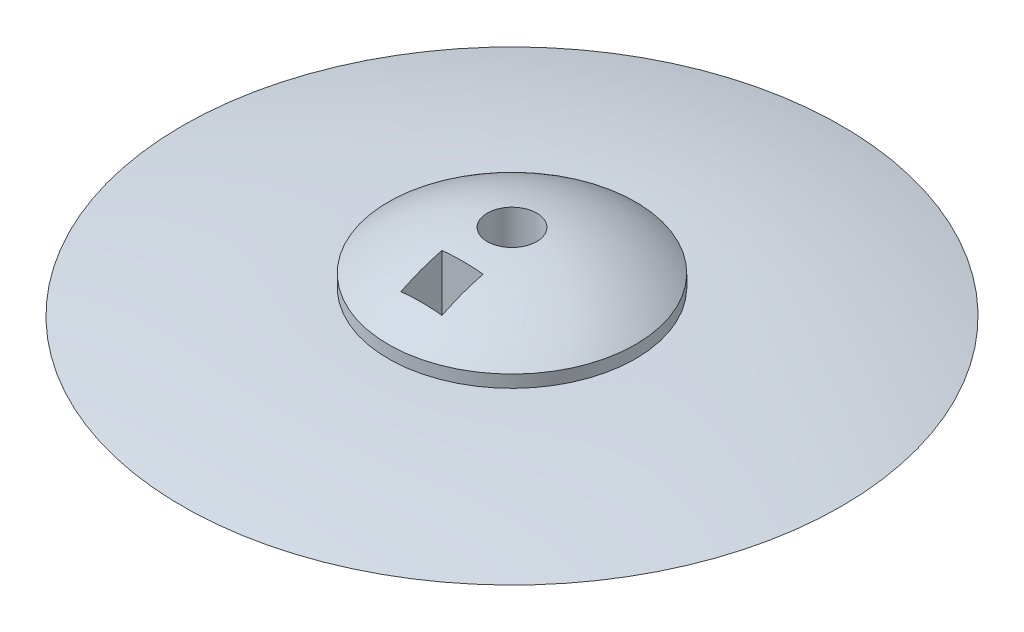
SolidWorks part; units mm, degrees
ref_plane "Front Plane" through (0, 0, 0) normal (0, 0, 1) x (1, 0, 0)
ref_plane "Top Plane" through (0, 0, 0) normal (0, 1, 0) x (1, 0, 0)
ref_plane "Right Plane" through (0, 0, 0) normal (1, 0, 0) x (0, 0, -1)
sketch "Sketch1" plane through (0, 0, 0) normal (0, 0, 1) x (1, 0, 0)
  line L0 (0, 0) -> (0, 19.05)
  line L1 (19.05, 12.7) -> (19.05, 10.795)
  line L2 (19.05, 3.175) -> (19.05, 1.27)
  line L3 (2.54, 0.635) -> (2.54, 0)
  line L4 (2.54, 0) -> (0, 0)
  line L5 (0, 19.05) -> (33.9184, 19.05) construction
  line L6 (2.54, 0.635) -> (17.0135, 0.635) construction
  line L7 (19.05, 3.175) -> (38.3157, 3.175) construction
  line L8 (19.05, 10.795) -> (52.4124, 10.795) construction
  line L9 (50.8, 6.985) -> (0, 6.985) construction
  arc A0 (0, 19.05) -> (19.05, 12.7) centre (0, -12.7) cw
  arc A1 (19.05, 10.795) -> (50.8, 6.985) centre (19.05, -123.4017) cw
  arc A2 (50.8, 6.985) -> (19.05, 3.175) centre (19.05, 137.3717) cw
  arc A3 (19.05, 1.27) -> (2.54, 0.635) centre (2.54, 215.5825) cw
  dimension "D1" = 2.54
  dimension "D2" = 50.8
  dimension "D3" = 1.27
  dimension "D4" = 1.905
  dimension "D5" = 12.7
  dimension "D6" = 19.05
  dimension "D7" = 19.05
  dimension "D8" = 0.635
revolve "Revolve1" add sketch "Sketch1" angle 360 about L0
sketch "Sketch2" plane through (0, 0, 0) normal (0, -1, 0) x (1, 0, 0)
  line L1 (3.175, 7.62) -> (-3.175, 7.62)
  line L2 (3.175, 7.62) -> (3.175, 13.97)
  line L3 (3.175, 13.97) -> (-3.175, 13.97)
  line L4 (-3.175, 7.62) -> (-3.175, 13.97)
  circle A0 centre (0, 0) radius 3.81
  point P7 (0, 7.62)
  dimension "D1" = 7.62
  dimension "D2" = 6.35
  dimension "D3" = 6.35
  dimension "D4" = 7.62
extrude "Cut-Extrude1" cut sketch "Sketch2" against normal through all
ref_plane "Plane1" through (0, 5.08, 0) normal (0, 1, 0) x (1, 0, 0)
sketch "Sketch3" plane through (0, 5.08, 0) normal (0, 1, 0) x (1, 0, 0)
  line L1 (0, -1.905) -> (0, -5.715) construction
  line L2 (0, -1.905) -> (0, -5.715)
  arc A2 (0, -5.715) -> (0, -1.905) centre (0, -3.81) ccw
  circle A4 centre (0, 0) radius 3.81 construction
  dimension "D1" = 3.81
revolve "Revolve4" add sketch "Sketch3" angle 360 about L1
